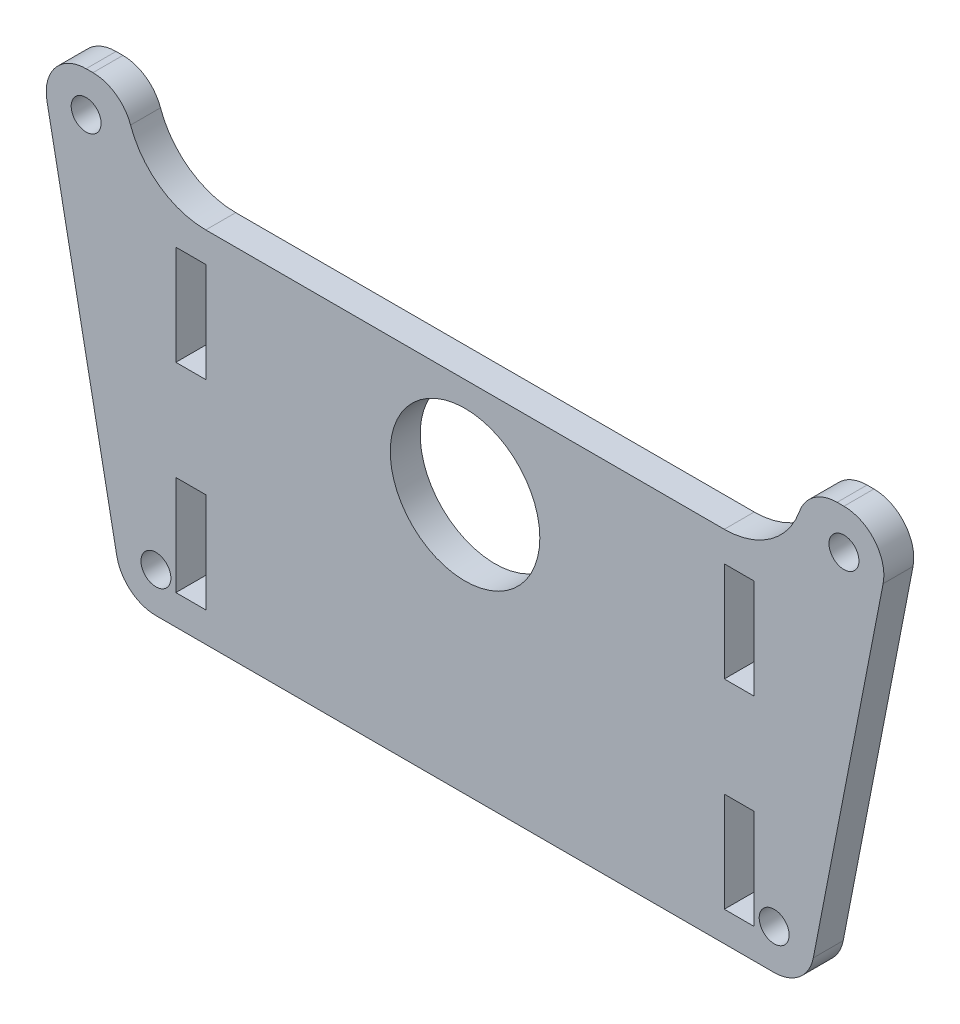
SolidWorks part; units mm, degrees
ref_plane "Front Plane" through (0, 0, 0) normal (0, 0, 1) x (1, 0, 0)
ref_plane "Top Plane" through (0, 0, 0) normal (0, 1, 0) x (1, 0, 0)
ref_plane "Right Plane" through (0, 0, 0) normal (1, 0, 0) x (0, 0, -1)
sketch "Sketch1" plane through (0, 0, 0) normal (0, 0, 1) x (1, 0, 0)
  line L0 (-41.9265, 19.1155) -> (-34.9265, -16.8845)
  line L1 (-31, -20.121) -> (31, -20.121)
  line L2 (34.9265, -16.8845) -> (41.9265, 19.1155)
  line L3 (38, 23.879) -> (37.3137, 23.879)
  line L4 (-26, 23.879) -> (26, 23.879) construction
  line L5 (0, 23.879) -> (0, -25.5478) construction
  line L6 (-26, 15.879) -> (26, 15.879)
  line L7 (-37.3137, 23.879) -> (-38, 23.879)
  line L8 (-29, 12.879) -> (-26, 12.879)
  line L9 (-29, 12.879) -> (-29, 2.879)
  line L10 (-29, 2.879) -> (-26, 2.879)
  line L11 (-26, 12.879) -> (-26, 2.879)
  line L12 (-29, -7.121) -> (-26, -7.121)
  line L13 (-29, -7.121) -> (-29, -17.121)
  line L14 (-29, -17.121) -> (-26, -17.121)
  line L15 (-26, -7.121) -> (-26, -17.121)
  line L16 (26, -7.121) -> (26, -17.121)
  line L17 (29, -17.121) -> (26, -17.121)
  line L18 (29, -7.121) -> (29, -17.121)
  line L19 (29, -7.121) -> (26, -7.121)
  line L20 (26, 12.879) -> (26, 2.879)
  line L21 (29, 2.879) -> (26, 2.879)
  line L22 (29, 12.879) -> (29, 2.879)
  line L23 (29, 12.879) -> (26, 12.879)
  line L24 (0, -55) -> (0, 55) construction
  circle A0 centre (38, 19.879) radius 1.5
  circle A1 centre (-38, 19.879) radius 1.5
  circle A2 centre (31, -16.121) radius 1.5
  circle A3 centre (-31, -16.121) radius 1.5
  arc A4 (31, -20.121) -> (34.9265, -16.8845) centre (31, -16.121) ccw
  arc A5 (-34.9265, -16.8845) -> (-31, -20.121) centre (-31, -16.121) ccw
  arc A6 (-41.9265, 19.1155) -> (-38, 23.879) centre (-38, 19.879) cw
  arc A7 (41.9265, 19.1155) -> (38, 23.879) centre (38, 19.879) ccw
  arc A8 (-33.5425, 21.2123) -> (-26, 15.879) centre (-26, 23.879) ccw
  arc A9 (26, 15.879) -> (33.5425, 21.2123) centre (26, 23.879) ccw
  arc A10 (37.3137, 23.879) -> (33.5425, 21.2123) centre (37.3137, 19.879) ccw
  arc A11 (-37.3137, 23.879) -> (-33.5425, 21.2123) centre (-37.3137, 19.879) cw
  circle A12 centre (0, 5.879) radius 7.5
  point P22 (0, 23.879)
  dimension "D1" = 3
  dimension "D3" = 3
  dimension "D7" = 3
  dimension "D8" = 3
  dimension "D9" = 4
  dimension "D10" = 4
  dimension "D17" = 4
  dimension "D18" = 4
  dimension "D19" = 4
  dimension "D21" = 8
  dimension "D23" = 4
  dimension "D20" = 15
  dimension "D2" = 76
  dimension "D4" = 62
  dimension "D5" = 36
  dimension "D6" = 7
  dimension "D11" = 4
  dimension "D12" = 4
  dimension "D13" = 4
  dimension "D14" = 4
  dimension "D15" = 4
  dimension "D16" = 36
  dimension "D22" = 10
  dimension "D24" = 3
  dimension "D25" = 10
  dimension "D26" = 10
  dimension "D27" = 3
  dimension "D28" = 26
  dimension "D29" = 31
extrude "Boss-Extrude1" add sketch "Sketch1" along normal blind 3
